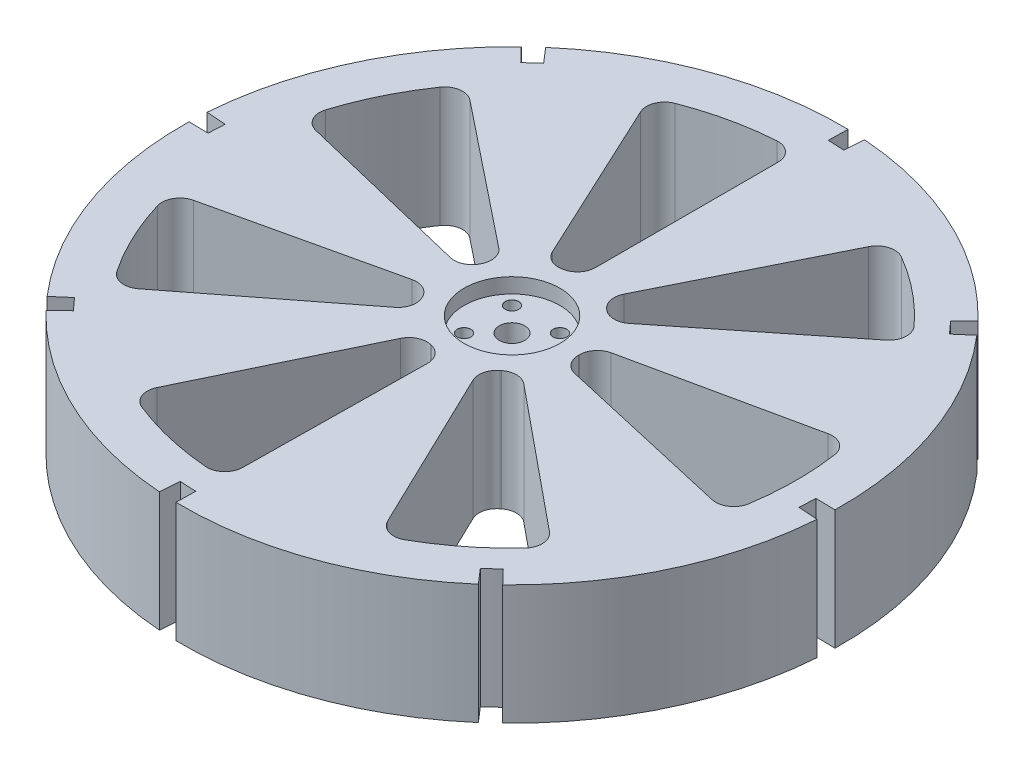
SolidWorks part; units mm, degrees
ref_plane "Front Plane" through (0, 0, 0) normal (0, 0, 1) x (1, 0, 0)
ref_plane "Top Plane" through (0, 0, 0) normal (0, 1, 0) x (1, 0, 0)
ref_plane "Right Plane" through (0, 0, 0) normal (1, 0, 0) x (0, 0, -1)
sketch "Sketch1" plane through (0, 0, 0) normal (0, 1, 0) x (1, 0, 0)
  circle A0 centre (0, 0) radius 110
  dimension "D1" = 220
extrude "Boss-Extrude1" add sketch "Sketch1" along normal blind 40
sketch "Sketch2" plane through (0, 40, 0) normal (0, 1, 0) x (1, 0, 0)
  line L0 (0, 0) -> (0, 95)
  line L1 (0, 0) -> (-40.1487, 86.0992)
  circle A2 centre (0, 0) radius 95
  circle A3 centre (0, 0) radius 22.5
  dimension "D1" = 45
  dimension "D3" = 190
  dimension "D2" = 25
extrude "Cut-Extrude1" cut sketch "Sketch2" against normal blind 40
fillet "Fillet1" radius 6 4 edges at (0, 20, -95) (-40.1487, 20, -86.0992) (0, 20, -22.5) (-9.5089, 20, -20.3919)
sketch "Sketch3" plane through (0, 40, 0) normal (0, 1, 0) x (1, 0, 0)
  circle A0 centre (0, 0) radius 4.25
  dimension "D1" = 8.5
extrude "Cut-Extrude2" cut sketch "Sketch3" against normal blind 40
pattern_circular "CirPattern1" count 7 over 360 about axis through (0, 0, 0) along (0, 1, 0) of "Fillet1", "Cut-Extrude1"
ref_plane "Plane1" through (0, 20, 0) normal (0, 1, 0) x (1, 0, 0)
sketch "Sketch4" plane through (0, 40, 0) normal (0, 1, 0) x (1, 0, 0)
  circle A0 centre (0, 0) radius 16
  dimension "D1" = 32
extrude "Cut-Extrude3" cut sketch "Sketch4" against normal blind 5
hole_wizard "M4 Clearance Hole1" positions "Sketch8" profile "Sketch6" hole size "M4" standard "ANSI Metric"
sketch "Sketch8" plane through (0, 35, 0) normal (0, 1, 0) x (1, 0, 0)
  point P0 (8, 8)
  point P2 (-8, 8)
  point P4 (-8, -8)
  point P6 (8, -8)
  dimension "D1" = 8
  dimension "D2" = 8
  dimension "D3" = 8
  dimension "D4" = 8
sketch "Sketch6" plane through (8, 35, -8) normal (1, 0, 0) x (0, 0, 1)
  line L0 (0, 0) -> (0, 14.3519)
  line L1 (0, 14.3519) -> (2.25, 13)
  line L2 (2.25, 13) -> (2.25, 0.025)
  line L3 (2.25, 0.025) -> (2.275, 0)
  line L5 (2.275, 0) -> (0, 0)
  line L6 (-2.25, 0.025) -> (-2.275, 0) construction
  line L10 (0, 14.3519) -> (-2.25, 13) construction
  line L11 (0, -6.35) -> (0, 107.95) construction
  dimension "Hole Dia." = 4.5
  dimension "Hole Depth" = 13
  dimension "Near C'Sink Dia." = 4.55
  dimension "Near C'Sink Angle" = 90
  dimension "Drill Angle" = 118
sketch "Sketch10" plane through (0, 40, 0) normal (0, 1, 0) x (1, 0, 0)
  line L0 (0, 0) -> (7.943, 109.7128)
  line L1 (0, 0) -> (2.1902, 109.9782)
  circle A0 centre (0, 0) radius 103.5
  circle A1 centre (0, 0) radius 110
  dimension "D1" = 3
  dimension "D2" = 207
extrude "Cut-Extrude4" cut sketch "Sketch10" against normal through all contours L0 A1 L1 A0
pattern_circular "CirPattern2" count 8 over 360 about axis through (0, 0, 0) along (0, 1, 0) of "Cut-Extrude4"
